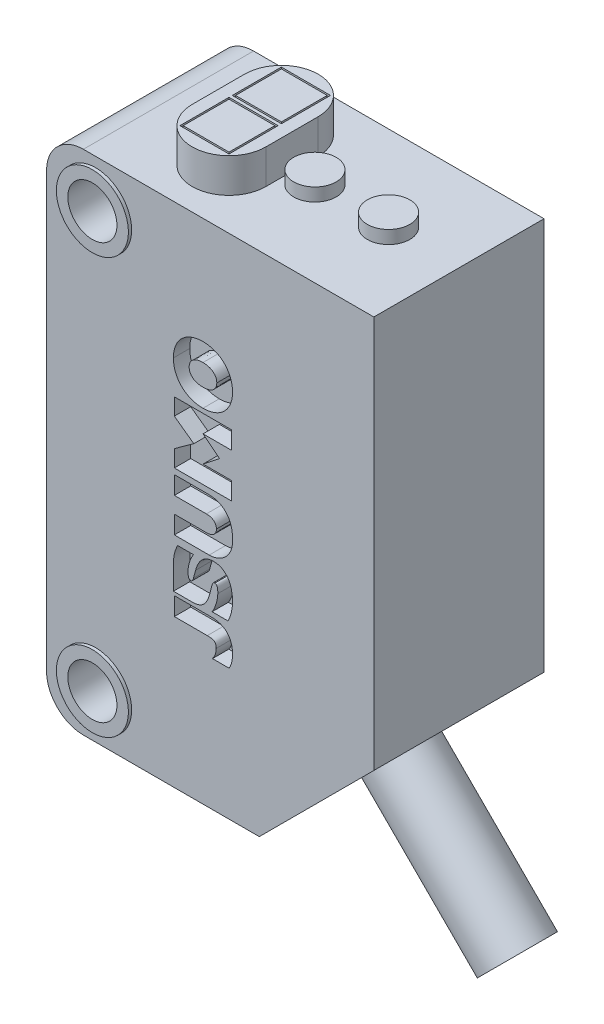
SolidWorks part; units mm, degrees
ref_plane "Alzado" through (0, 0, 0) normal (0, 0, 1) x (1, 0, 0)
ref_plane "Planta" through (0, 0, 0) normal (0, 1, 0) x (1, 0, 0)
ref_plane "Vista lateral" through (0, 0, 0) normal (1, 0, 0) x (0, 0, -1)
ref_plane "Plano1" through (0, 0, 5.2) normal (0, 0, 1) x (1, 0, 0)
sketch "Croquis1" plane through (0, 0, 5.2) normal (0, 0, 1) x (1, 0, 0)
  line L0 (17, 28.2) -> (-3, 28.2)
  line L1 (-3, 28.2) -> (-3, -2.8)
  line L2 (-3, -2.8) -> (10, -2.8)
  line L3 (10, -2.8) -> (17, 4.2)
  line L4 (17, 4.2) -> (17, 28.2)
extrude "Saliente-Extruir1" add sketch "Croquis1" against normal blind 10.4
sketch "Croquis2" plane through (0, 28.2, 0) normal (0, 1, 0) x (-1, 0, 0)
  line L0 (-6.8, -1.6) -> (-6.8, 1.6)
  line L1 (-2.3, 1.6) -> (-2.3, -1.6)
  arc A0 (-2.3, -1.6) -> (-6.8, -1.6) centre (-4.55, -1.6) cw
  arc A1 (-6.8, 1.6) -> (-2.3, 1.6) centre (-4.55, 1.6) cw
extrude "Saliente-Extruir2" add sketch "Croquis2" along normal blind 2.1
sketch "Croquis3" plane through (0, 30.3, 0) normal (0, 1, 0) x (-1, 0, 0)
  line L0 (-6.05, 0.1) -> (-3.05, 0.1)
  line L1 (-3.05, 0.1) -> (-3.05, 3.1)
  line L2 (-3.05, 3.1) -> (-6.05, 3.1)
  line L3 (-6.05, 3.1) -> (-6.05, 0.1)
extrude "Cortar-Extruir1" cut sketch "Croquis3" against normal blind 1
sketch "Croquis4" plane through (0, 29.3, 0) normal (0, 1, 0) x (-1, 0, 0)
  line L0 (-5.95, 0.2) -> (-5.95, 3)
  line L1 (-5.95, 3) -> (-3.15, 3)
  line L2 (-3.15, 3) -> (-3.15, 0.2)
  line L3 (-3.15, 0.2) -> (-5.95, 0.2)
extrude "Saliente-Extruir3" add sketch "Croquis4" along normal blind 1
sketch "Croquis5" plane through (0, 30.3, 0) normal (0, 1, 0) x (-1, 0, 0)
  line L0 (-6.05, -0.1) -> (-6.05, -3.1)
  line L1 (-6.05, -3.1) -> (-3.05, -3.1)
  line L2 (-3.05, -3.1) -> (-3.05, -0.1)
  line L3 (-3.05, -0.1) -> (-6.05, -0.1)
extrude "Cortar-Extruir2" cut sketch "Croquis5" against normal blind 1
sketch "Croquis6" plane through (0, 29.3, 0) normal (0, 1, 0) x (-1, 0, 0)
  line L0 (-5.95, -3) -> (-5.95, -0.2)
  line L1 (-5.95, -0.2) -> (-3.15, -0.2)
  line L2 (-3.15, -0.2) -> (-3.15, -3)
  line L3 (-3.15, -3) -> (-5.95, -3)
extrude "Saliente-Extruir4" add sketch "Croquis6" along normal blind 1
ref_plane "Plano2" through (0, 0, 2.2) normal (0, 0, 1) x (1, 0, 0)
sketch "Croquis7" plane through (0, 0, 2.2) normal (0, 0, 1) x (1, 0, 0)
  spline S0 degree 3 poles (6.5569, 18.1488) (6.4837, 18.1508) (6.3377, 18.1548) (6.1212, 18.1886) (5.9101, 18.2449) (5.7077, 18.3271) (5.5164, 18.432) (5.3402, 18.5608) (5.1827, 18.7115) (5.0478, 18.8823) (4.9376, 19.0698) (4.8519, 19.2693) (4.7929, 19.4783) (4.7583, 19.6931) (4.7543, 19.8378) (4.7523, 19.9104) knots 0 0 0 0 0.077583 0.154906 0.231879 0.30891 0.386121 0.462825 0.539834 0.616769 0.693013 0.769892 0.846517 0.923009 1 1 1 1
  spline S1 degree 3 poles (4.7523, 19.9104) (4.7552, 19.997) (4.761, 20.1697) (4.8109, 20.4246) (4.8961, 20.6692) (5.0168, 20.8978) (5.172, 21.1048) (5.3584, 21.283) (5.5702, 21.43) (5.8016, 21.5436) (6.0463, 21.6237) (6.3, 21.6707) (6.4711, 21.6759) (6.5569, 21.6786) knots 0 0 0 0 0.091665 0.182879 0.273878 0.36517 0.455665 0.546797 0.637127 0.72777 0.8189 0.909173 1 1 1 1
  spline S2 degree 3 poles (6.5569, 21.6786) (6.6301, 21.6766) (6.7765, 21.6726) (6.9934, 21.6387) (7.2049, 21.5824) (7.4079, 21.5004) (7.5993, 21.3951) (7.775, 21.2653) (7.931, 21.1125) (8.065, 20.9404) (8.1754, 20.7522) (8.2626, 20.5528) (8.3229, 20.3435) (8.3586, 20.1283) (8.3627, 19.9832) (8.3647, 19.9104) knots 0 0 0 0 0.077553 0.154856 0.23183 0.308876 0.386038 0.462576 0.539436 0.616515 0.692911 0.769779 0.846411 0.922962 1 1 1 1
  spline S3 degree 3 poles (8.3647, 19.9104) (8.3626, 19.8372) (8.3583, 19.6911) (8.322, 19.475) (8.2613, 19.2652) (8.1727, 19.0656) (8.0613, 18.8782) (7.9262, 18.7072) (7.7691, 18.5561) (7.5927, 18.4277) (7.4009, 18.3236) (7.1986, 18.243) (6.9885, 18.1873) (6.7738, 18.1544) (6.6294, 18.1507) (6.5569, 18.1488) knots 0 0 0 0 0.077586 0.154877 0.231765 0.308711 0.38586 0.462416 0.539246 0.616397 0.693033 0.77021 0.846843 0.92315 1 1 1 1
extrude "Cortar-Extruir3" cut sketch "Croquis7" against normal blind 1 from surface at 3 starting at face at (7.6, 11, 5.2)
ref_plane "Plano3" through (0, 0, 7.2) normal (0, 0, -1) x (0, 1, 0)
sketch "Croquis8" plane through (0, 0, 7.2) normal (0, 0, -1) x (0, 1, 0)
  spline S0 degree 3 poles (19.9104, 7.403) (19.9554, 7.4005) (20.0452, 7.3956) (20.1742, 7.3523) (20.2885, 7.2803) (20.3837, 7.1847) (20.4587, 7.0731) (20.5122, 6.9502) (20.5464, 6.8214) (20.5652, 6.6897) (20.5671, 6.6013) (20.5681, 6.5569) knots 0 0 0 0 0.112118 0.223579 0.335249 0.446416 0.557621 0.668998 0.779436 0.889269 1 1 1 1
  spline S1 degree 3 poles (20.5681, 6.5569) (20.5671, 6.5125) (20.5652, 6.4238) (20.5462, 6.2918) (20.5119, 6.1628) (20.4578, 6.0399) (20.382, 5.9287) (20.2863, 5.8342) (20.1723, 5.7635) (20.0442, 5.7215) (19.9551, 5.7166) (19.9104, 5.7141) knots 0 0 0 0 0.111022 0.221544 0.332555 0.443846 0.555736 0.667127 0.777586 0.888274 1 1 1 1
  spline S2 degree 3 poles (19.9104, 5.7141) (19.8658, 5.7165) (19.7769, 5.7213) (19.649, 5.7637) (19.5359, 5.8351) (19.4421, 5.9305) (19.3688, 6.042) (19.3166, 6.1647) (19.2836, 6.2932) (19.2654, 6.4245) (19.2635, 6.5127) (19.2626, 6.5569) knots 0 0 0 0 0.111874 0.222944 0.334151 0.445119 0.556478 0.667657 0.778571 0.889013 1 1 1 1
  spline S3 degree 3 poles (19.2626, 6.5569) (19.2635, 6.6011) (19.2654, 6.6895) (19.2837, 6.8211) (19.3168, 6.9499) (19.369, 7.0732) (19.4425, 7.1854) (19.5364, 7.2813) (19.6493, 7.3531) (19.7769, 7.3955) (19.8657, 7.4005) (19.9104, 7.403) knots 0 0 0 0 0.111002 0.221461 0.332406 0.443751 0.555604 0.667102 0.777567 0.88824 1 1 1 1
extrude "Saliente-Extruir5" add sketch "Croquis8" against normal blind 1 from surface at 3 starting at face at (6.5577, 19.912, 4.2)
sketch "Croquis9" plane through (-3, 0, 0) normal (-1, 0, 0) x (0, 0, 1)
  line L0 (-3.6, 5) -> (3.6, 5)
  line L1 (3.6, 5) -> (3.6, 20.4)
  line L2 (3.6, 20.4) -> (-3.6, 20.4)
  line L3 (-3.6, 20.4) -> (-3.6, 5)
extrude "Cortar-Extruir4" cut sketch "Croquis9" against normal blind 1
sketch "Croquis10" plane through (-2, 0, 0) normal (-1, 0, 0) x (0, 0, 1)
  line L0 (-3.5, 5.1) -> (-3.5, 20.3)
  line L1 (-3.5, 20.3) -> (3.5, 20.3)
  line L2 (3.5, 20.3) -> (3.5, 5.1)
  line L3 (3.5, 5.1) -> (-3.5, 5.1)
extrude "Saliente-Extruir6" add sketch "Croquis10" along normal blind 1
sketch "Croquis11" plane through (0, 0, 2.2) normal (0, 0, 1) x (1, 0, 0)
  line L0 (7.1121, 9.0667) -> (6.9733, 8.5313)
  line L1 (5.0002, 10.111) -> (5.9818, 10.111)
  line L2 (5.9719, 8.8518) -> (6.1074, 9.3509)
  line L3 (8.0904, 7.6587) -> (7.1154, 7.6587)
  arc A0 (8.3647, 8.8287) -> (8.0904, 7.6587) centre (5.8115, 8.8102) cw
  spline S0 degree 3 poles (7.2807, 9.2551) (7.2755, 9.255) (7.2652, 9.2548) (7.2499, 9.2532) (7.2347, 9.2504) (7.2199, 9.246) (7.2058, 9.2398) (7.1926, 9.2317) (7.1809, 9.2215) (7.1711, 9.2095) (7.1631, 9.1962) (7.1556, 9.1827) (7.1488, 9.1687) (7.1424, 9.1546) (7.1366, 9.1402) (7.131, 9.1257) (7.1259, 9.1111) (7.121, 9.0964) (7.1164, 9.0816) (7.1136, 9.0716) (7.1121, 9.0667) knots 0 0 0 0 0.055408 0.110811 0.166162 0.221319 0.27682 0.332262 0.387543 0.442988 0.498534 0.554262 0.610031 0.665753 0.721428 0.777124 0.832843 0.888576 0.944304 1 1 1 1
  spline S1 degree 3 poles (6.9733, 8.5313) (6.9559, 8.4685) (6.9212, 8.3432) (6.8496, 8.1615) (6.7584, 7.9887) (6.6398, 7.8325) (6.4898, 7.705) (6.3124, 7.6204) (6.1225, 7.5733) (5.9274, 7.5614) (5.7321, 7.5633) (5.5362, 7.5628) (5.3402, 7.5629) (5.1443, 7.5629) (4.9483, 7.5629) (4.8177, 7.5629) (4.7523, 7.5629) knots 0 0 0 0 0.071468 0.142587 0.213863 0.285264 0.356574 0.427679 0.498905 0.569946 0.641582 0.713266 0.784949 0.856633 0.928316 1 1 1 1
  spline S2 degree 3 poles (4.7523, 7.5629) (4.7523, 7.6413) (4.7523, 7.7981) (4.7523, 8.0333) (4.7524, 8.2685) (4.7523, 8.5037) (4.7526, 8.7388) (4.7514, 8.9739) (4.7567, 9.209) (4.7807, 9.4431) (4.8329, 9.6724) (4.9053, 9.8961) (4.9686, 10.0394) (5.0002, 10.111) knots 0 0 0 0 0.090975 0.18195 0.272925 0.363901 0.454876 0.545848 0.636727 0.727592 0.818347 0.909177 1 1 1 1
  spline S3 degree 3 poles (5.9818, 10.111) (5.9414, 10.0457) (5.8607, 9.9153) (5.7661, 9.7049) (5.6951, 9.4855) (5.6524, 9.2579) (5.6473, 9.104) (5.6447, 9.027) knots 0 0 0 0 0.199872 0.399203 0.599389 0.799522 1 1 1 1
  spline S4 degree 3 poles (5.6447, 9.027) (5.6449, 9.0061) (5.6454, 8.9643) (5.6501, 8.9018) (5.6591, 8.8396) (5.6731, 8.7782) (5.6939, 8.719) (5.7367, 8.6677) (5.7789, 8.6605) (5.8, 8.6568) knots 0 0 0 0 0.1431 0.285746 0.42843 0.572117 0.715442 0.857868 1 1 1 1
  spline S5 degree 3 poles (5.8, 8.6568) (5.8064, 8.657) (5.819, 8.6573) (5.8379, 8.6599) (5.8564, 8.6646) (5.874, 8.6719) (5.8902, 8.682) (5.9044, 8.6949) (5.9159, 8.7102) (5.9257, 8.7265) (5.9345, 8.7435) (5.9424, 8.761) (5.9496, 8.7787) (5.956, 8.7967) (5.9618, 8.8149) (5.9671, 8.8333) (5.9703, 8.8457) (5.9719, 8.8518) knots 0 0 0 0 0.066408 0.132903 0.199147 0.26576 0.332201 0.398718 0.465217 0.532037 0.598964 0.665842 0.732619 0.799443 0.86631 0.933183 1 1 1 1
  spline S6 degree 3 poles (6.1074, 9.3509) (6.1248, 9.4087) (6.1595, 9.5242) (6.227, 9.6922) (6.3091, 9.8538) (6.4107, 10.0046) (6.5352, 10.1375) (6.6829, 10.2441) (6.8487, 10.3188) (7.0262, 10.3617) (7.1473, 10.3665) (7.208, 10.3688) knots 0 0 0 0 0.111151 0.221808 0.332849 0.444308 0.55549 0.666318 0.777362 0.888361 1 1 1 1
  spline S7 degree 3 poles (7.208, 10.3688) (7.2743, 10.3662) (7.4064, 10.361) (7.5998, 10.3131) (7.7776, 10.2253) (7.9348, 10.1049) (8.0668, 9.9568) (8.1705, 9.7879) (8.2486, 9.6056) (8.3034, 9.4157) (8.339, 9.2218) (8.3609, 9.0259) (8.3634, 8.8945) (8.3647, 8.8287) knots 0 0 0 0 0.091618 0.182415 0.273062 0.363956 0.454492 0.545705 0.636789 0.727809 0.818436 0.908997 1 1 1 1
  spline S8 degree 3 poles (7.1154, 7.6587) (7.1558, 7.7278) (7.2366, 7.8658) (7.3266, 8.0888) (7.3984, 8.3176) (7.4536, 8.5523) (7.4617, 8.7124) (7.4657, 8.7924) knots 0 0 0 0 0.199963 0.399423 0.599832 0.800046 1 1 1 1
  spline S9 degree 3 poles (7.4657, 8.7924) (7.4657, 8.8127) (7.4655, 8.8535) (7.4632, 8.9145) (7.4588, 8.9754) (7.4512, 9.036) (7.4403, 9.0962) (7.4232, 9.1553) (7.3924, 9.2088) (7.3428, 9.2496) (7.3014, 9.2532) (7.2807, 9.2551) knots 0 0 0 0 0.111213 0.22228 0.333176 0.444018 0.555293 0.666762 0.777925 0.888647 1 1 1 1
extrude "Cortar-Extruir5" cut sketch "Croquis11" against normal blind 1 from surface at 3 starting at face at (6.5577, 19.912, 5.2)
sketch "Croquis12" plane through (0, 0, 5.2) normal (0, 0, 1) x (1, 0, 0)
  line L0 (8.3085, 15.1974) -> (6.5635, 15.1974)
  line L1 (6.5635, 15.1974) -> (7.5695, 15.9956)
  line L2 (7.5695, 15.9956) -> (6.5635, 16.7971)
  line L3 (6.5635, 16.7971) -> (8.3085, 16.7971)
  line L4 (8.3085, 16.7971) -> (8.3085, 17.8811)
  line L5 (8.3085, 17.8811) -> (4.8085, 17.8811)
  line L6 (4.8085, 17.8811) -> (4.8085, 16.8566)
  line L7 (4.8085, 16.8566) -> (5.9983, 15.994)
  line L8 (5.9983, 15.994) -> (4.8085, 15.138)
  line L9 (4.8085, 15.138) -> (4.8085, 14.1134)
  line L10 (4.8085, 14.1134) -> (8.3085, 14.1134)
  line L11 (8.3085, 14.1134) -> (8.3085, 15.1974)
extrude "Cortar-Extruir6" cut sketch "Croquis12" against normal blind 1
sketch "Croquis13" plane through (0, 0, 2.2) normal (0, 0, 1) x (1, 0, 0)
  line L0 (4.8085, 10.5704) -> (4.8085, 11.671)
  line L1 (4.8085, 11.671) -> (6.7651, 11.671)
  line L2 (6.7651, 12.6625) -> (4.8085, 12.6625)
  line L3 (4.8085, 12.6625) -> (4.8085, 13.7631)
  line L4 (4.8085, 13.7631) -> (6.8609, 13.7631)
  line L5 (8.3647, 10.5704) -> (4.8085, 10.5704)
  spline S0 degree 3 poles (6.7651, 11.671) (6.7981, 11.6717) (6.8639, 11.6731) (6.9621, 11.6873) (7.0579, 11.7132) (7.1487, 11.7543) (7.2297, 11.8124) (7.297, 11.8857) (7.3462, 11.972) (7.3749, 12.0675) (7.3782, 12.1336) (7.3798, 12.1668) knots 0 0 0 0 0.111168 0.221966 0.333409 0.44482 0.556141 0.66724 0.777653 0.888318 1 1 1 1
  spline S1 degree 3 poles (7.3798, 12.1668) (7.3782, 12.2001) (7.3751, 12.2666) (7.3465, 12.3631) (7.297, 12.4502) (7.2289, 12.5236) (7.1472, 12.5811) (7.0563, 12.6214) (6.9609, 12.6467) (6.8634, 12.6604) (6.798, 12.6618) (6.7651, 12.6625) knots 0 0 0 0 0.11211 0.223573 0.335329 0.446725 0.557966 0.669267 0.779636 0.889376 1 1 1 1
  spline S2 degree 3 poles (6.8609, 13.7631) (6.9465, 13.7604) (7.1173, 13.755) (7.3697, 13.7044) (7.6096, 13.6137) (7.8286, 13.4797) (8.0136, 13.302) (8.1594, 13.0913) (8.2628, 12.8573) (8.3288, 12.6115) (8.3628, 12.3594) (8.3652, 12.1049) (8.3646, 11.8495) (8.3647, 11.5937) (8.3647, 11.3379) (8.3647, 11.0821) (8.3647, 10.8263) (8.3647, 10.6557) (8.3647, 10.5704) knots 0 0 0 0 0.062833 0.125447 0.188128 0.250468 0.312777 0.375206 0.437599 0.499828 0.561636 0.624021 0.686685 0.749348 0.812011 0.874674 0.937337 1 1 1 1
extrude "Cortar-Extruir7" cut sketch "Croquis13" against normal blind 1 from surface at 3 starting at face at (6.5969, 15.9968, 5.2)
sketch "Croquis14" plane through (0, 0, 2.2) normal (0, 0, 1) x (1, 0, 0)
  line L0 (6.8213, 6.2508) -> (4.8085, 6.2508)
  line L1 (4.8085, 6.2508) -> (4.8085, 7.358)
  line L2 (4.8085, 7.358) -> (7.0658, 7.358)
  line L3 (8.1532, 5.1899) -> (7.1386, 5.1899)
  spline S0 degree 3 poles (7.0658, 7.358) (7.1445, 7.3558) (7.3014, 7.3516) (7.5336, 7.3074) (7.7543, 7.2241) (7.9546, 7.0985) (8.1199, 6.929) (8.2406, 6.7256) (8.3159, 6.5031) (8.3579, 6.2726) (8.3624, 6.1172) (8.3647, 6.0393) knots 0 0 0 0 0.11179 0.223069 0.334514 0.445622 0.556592 0.668011 0.779099 0.889223 1 1 1 1
  spline S1 degree 3 poles (8.3647, 6.0393) (8.364, 5.997) (8.3627, 5.9124) (8.3512, 5.786) (8.3316, 5.6608) (8.3027, 5.5374) (8.2643, 5.4168) (8.2199, 5.2977) (8.1754, 5.2258) (8.1532, 5.1899) knots 0 0 0 0 0.143186 0.28619 0.428976 0.571731 0.714658 0.85731 1 1 1 1
  spline S2 degree 3 poles (7.1386, 5.1899) (7.1648, 5.2291) (7.2172, 5.3072) (7.2825, 5.4323) (7.3329, 5.564) (7.3616, 5.7028) (7.3649, 5.797) (7.3666, 5.8443) knots 0 0 0 0 0.200574 0.400315 0.599104 0.798946 1 1 1 1
  spline S3 degree 3 poles (7.3666, 5.8443) (7.3661, 5.8685) (7.3652, 5.9169) (7.3548, 5.9888) (7.3342, 6.0583) (7.2993, 6.1225) (7.2447, 6.1719) (7.179, 6.2032) (7.1095, 6.2244) (7.0381, 6.2374) (6.966, 6.2457) (6.8937, 6.2501) (6.8454, 6.2506) (6.8213, 6.2508) knots 0 0 0 0 0.091366 0.182285 0.272778 0.363531 0.453948 0.544845 0.635776 0.727081 0.818083 0.908979 1 1 1 1
extrude "Cortar-Extruir8" cut sketch "Croquis14" against normal blind 1 from surface at 3 starting at face at (6.5969, 15.9968, 5.2)
ref_plane "Plano4" through (0, 25.4, 0) normal (0, 1, 0) x (1, 0, 0)
sketch "Croquis15" plane through (0, 25.4, 0) normal (0, 1, 0) x (1, 0, 0)
  line L0 (2.2, 5.4) -> (0, 5.4)
  line L1 (0, 5.4) -> (0, 5.2)
  line L2 (0, 5.2) -> (2.2, 5.2)
  line L3 (2.2, 5.2) -> (2.2, 5.4)
  line L4 (0, 5.4) -> (0, 5.2) construction
revolve "Revolución1" add sketch "Croquis15" angle 360 about L4
sketch "Croquis16" plane through (0, 0, 0) normal (0, 1, 0) x (1, 0, 0)
  line L0 (2.2, 5.4) -> (0, 5.4)
  line L1 (0, 5.4) -> (0, 5.2)
  line L2 (0, 5.2) -> (2.2, 5.2)
  line L3 (2.2, 5.2) -> (2.2, 5.4)
  line L4 (0, 5.4) -> (0, 5.2) construction
revolve "Revolución2" add sketch "Croquis16" angle 360 about L4
sketch "Croquis17" plane through (0, 0, 0) normal (0, 0, 1) x (1, 0, 0)
  line L0 (9.5, 29) -> (8.2, 29)
  line L1 (8.2, 29) -> (8.2, 28.2)
  line L2 (8.2, 28.2) -> (9.5, 28.2)
  line L3 (9.5, 28.2) -> (9.5, 29)
  line L4 (8.2, 29) -> (8.2, 28.2) construction
revolve "Revolución3" add sketch "Croquis17" angle 360 about L4
sketch "Croquis18" plane through (0, 0, 0) normal (0, 0, 1) x (1, 0, 0)
  line L0 (14, 29) -> (12.7, 29)
  line L1 (12.7, 29) -> (12.7, 28.2)
  line L2 (12.7, 28.2) -> (14, 28.2)
  line L3 (14, 28.2) -> (14, 29)
  line L4 (12.7, 29) -> (12.7, 28.2) construction
revolve "Revolución4" add sketch "Croquis18" angle 360 about L4
sketch "Croquis19" plane through (0, 0, 0) normal (0, 0, 1) x (1, 0, 0)
  line L0 (13.5, 0.7) -> (12.0858, -0.7142)
  line L1 (12.0858, -0.7142) -> (19.1569, -7.7853)
  line L2 (19.1569, -7.7853) -> (20.5711, -6.3711)
  line L3 (20.5711, -6.3711) -> (13.5, 0.7)
  line L4 (20.5711, -6.3711) -> (13.5, 0.7) construction
revolve "Revolución5" add sketch "Croquis19" angle 360 about L4
ref_plane "Plano5" through (0, 0, 0) normal (0, -1, 0) x (1, 0, 0)
sketch "Croquis20" plane through (0, 0, 0) normal (0, -1, 0) x (1, 0, 0)
  line L0 (2.2, 5.4) -> (0, 5.4)
  line L1 (0, 5.4) -> (0, 5.2)
  line L2 (0, 5.2) -> (2.2, 5.2)
  line L3 (2.2, 5.2) -> (2.2, 5.4)
  line L4 (0, 5.4) -> (0, 5.2) construction
revolve "Revolución6" add sketch "Croquis20" angle 360 about L4
ref_plane "Plano6" through (0, 25.4, 0) normal (0, -1, 0) x (1, 0, 0)
sketch "Croquis21" plane through (0, 25.4, 0) normal (0, -1, 0) x (1, 0, 0)
  line L0 (2.2, 5.4) -> (0, 5.4)
  line L1 (0, 5.4) -> (0, 5.2)
  line L2 (0, 5.2) -> (2.2, 5.2)
  line L3 (2.2, 5.2) -> (2.2, 5.4)
  line L4 (0, 5.4) -> (0, 5.2) construction
revolve "Revolución7" add sketch "Croquis21" angle 360 about L4
hole_wizard "Diámetro de taladro Ø3.0 (3)1" positions "Croquis23" profile "Croquis22" hole size "Ø3.0" standard "Ansi Metric"
sketch "Croquis23" plane through (0, 0, 5.4) normal (0, 0, 1) x (1, 0, 0)
  point P0 (0, 0)
  point P1 (0, 25.4)
sketch "Croquis22" plane through (0, 0, 5.4) normal (1, 0, 0) x (0, -1, 0)
  line L0 (0, 0) -> (0, 10.8)
  line L1 (0, 10.8) -> (1.5, 10.8)
  line L2 (1.5, 10.8) -> (1.5, 0)
  line L5 (1.5, 0) -> (0, 0)
  line L11 (0, -6.35) -> (0, 107.95) construction
  dimension "Diámetro de taladro hasta el siguiente" = 3
  dimension "Profundidad de taladro hasta el siguiente" = 10.8
chamfer "Chaflán1" distance 0.0186 angle 51.457 1 edges at (7.5695, 15.9956, 4.7)
fillet "Redondeo4" radius 1.4274 1 edges at (8.3647, 10.5704, 4.7)
fillet "Redondeo5" radius 2.25 2 edges at (-3, 28.2, 0) (-3, -2.8, 0)
